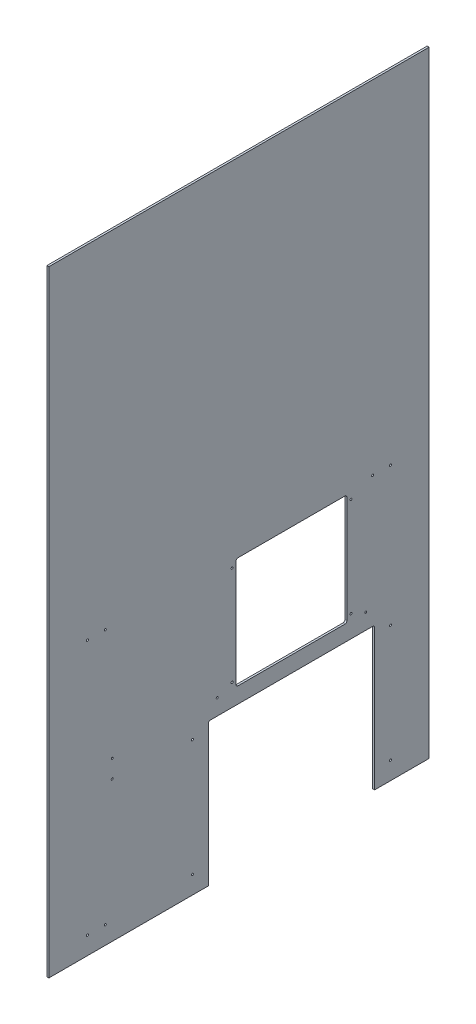
SolidWorks part; units mm, degrees
material "PC High Viscosity"
ref_plane "Front Plane" through (0, 0, 0) normal (0, 0, 1) x (1, 0, 0)
ref_plane "Top Plane" through (0, 0, 0) normal (0, 1, 0) x (1, 0, 0)
ref_plane "Right Plane" through (0, 0, 0) normal (1, 0, 0) x (0, 0, -1)
sketch "Sketch1" plane through (0, 0, 0) normal (1, 0, 0) x (0, 0, -1)
  line L1 (0, 0) -> (1219.2, 0)
  line L2 (0, 0) -> (0, 1974.85)
  line L3 (0, 1974.85) -> (1219.2, 1974.85)
  line L4 (1219.2, 0) -> (1219.2, 1974.85)
  dimension "D1" = 1974.85
  dimension "D2" = 1219.2
extrude "Boss-Extrude1" add sketch "Sketch1" along normal blind 6.35
sketch "Sketch2" plane through (6.35, 0, 0) normal (1, 0, 0) x (0, 0, -1)
  line L0 (0, 0) -> (1219.2, 0) construction
  line L1 (1044.575, 0) -> (511.175, 0)
  line L2 (1044.575, 0) -> (1044.575, 457.2)
  line L3 (1044.575, 457.2) -> (511.175, 457.2)
  line L4 (511.175, 0) -> (511.175, 457.2)
  line L5 (1219.2, 0) -> (1219.2, 1974.85) construction
  line L6 (955.675, 508) -> (600.075, 508)
  line L7 (955.675, 508) -> (955.675, 863.6)
  line L8 (955.675, 863.6) -> (600.075, 863.6)
  line L9 (600.075, 508) -> (600.075, 863.6)
  dimension "D1" = 174.625
  dimension "D2" = 708.025
  dimension "D3" = 457.2
  dimension "D4" = 508
  dimension "D5" = 355.6
  dimension "D6" = 355.6
  dimension "D7" = 263.525
extrude "Cut-Extrude1" cut sketch "Sketch2" against normal through all
fillet "Fillet1" radius 6.35 6 edges at (3.175, 457.2, -1044.575) (3.175, 457.2, -511.175) (3.175, 508, -955.675) (3.175, 508, -600.075) (3.175, 863.6, -955.675) (3.175, 863.6, -600.075)
hole_wizard "1/4 (0.25) Diameter Hole1" positions "Sketch3" profile "Sketch4" hole size "1/4" standard "ANSI Inch" end condition through all
sketch "Sketch3" plane through (6.35, 0, 0) normal (1, 0, 0) x (0, 0, -1)
  line L0 (1044.575, 0) -> (1219.2, 0) construction
  line L1 (0, 0) -> (511.175, 0) construction
  line L2 (1219.2, 0) -> (1219.2, 1974.85) construction
  point P0 (1095.375, 57.15)
  point P2 (1095.375, 431.8)
  point P4 (1095.375, 876.3)
  point P6 (968.375, 844.55)
  point P8 (587.375, 844.55)
  point P10 (587.375, 527.05)
  point P12 (968.375, 527.05)
  point P14 (1016, 508)
  point P16 (1038.225, 876.3)
  point P18 (539.75, 508)
  point P20 (460.375, 431.8)
  point P22 (460.375, 57.15)
  point P24 (180.975, 876.3)
  point P26 (203.2, 508)
  point P28 (203.2, 450.85)
  point P30 (123.825, 876.3)
  point P32 (180.975, 57.15)
  point P34 (123.825, 57.15)
  dimension "D1" = 57.15
  dimension "D2" = 431.8
  dimension "D3" = 508
  dimension "D4" = 527.05
  dimension "D5" = 844.55
  dimension "D6" = 876.3
  dimension "D7" = 450.85
  dimension "D8" = 123.825
  dimension "D9" = 180.975
  dimension "D10" = 203.2
  dimension "D11" = 250.825
  dimension "D12" = 631.825
  dimension "D13" = 679.45
  dimension "D14" = 758.825
  dimension "D15" = 1016
  dimension "D16" = 1038.225
  dimension "D17" = 1095.375
sketch "Sketch4" plane through (6.35, 57.15, -1095.375) normal (0, 1, 0) x (0, 0, -1)
  line L0 (0, 0) -> (0, 6.35)
  line L1 (0, 6.35) -> (3.175, 6.35)
  line L2 (3.175, 6.35) -> (3.175, 0)
  line L5 (3.175, 0) -> (0, 0)
  line L11 (0, -6.35) -> (0, 107.95) construction
  dimension "Thru Hole Dia." = 6.35
  dimension "Thru Hole Depth" = 6.35
